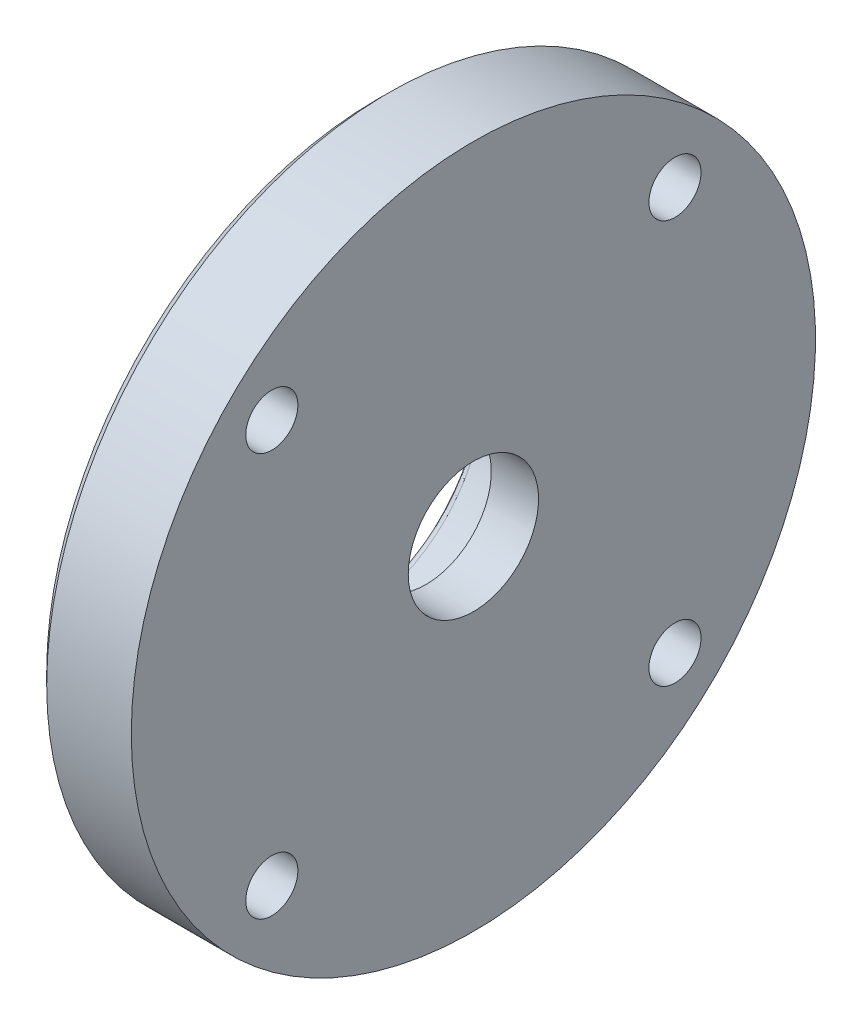
SolidWorks part; units mm, degrees
material "Chrome Stainless Steel"
ref_plane "Front" through (0, 0, 0) normal (0, 0, 1) x (1, 0, 0)
ref_plane "Top" through (0, 0, 0) normal (0, 1, 0) x (1, 0, 0)
ref_plane "Right" through (0, 0, 0) normal (1, 0, 0) x (0, 0, -1)
sketch "Sketch1" plane through (0, 0, 0) normal (0, 0, 1) x (1, 0, 0)
  line L0 (0, 0) -> (13.9806, 0) construction
  line L1 (0, 0) -> (0, 20.2929)
  line L2 (0, 20.2929) -> (0.7071, 21)
  line L3 (0.7071, 21) -> (5.9, 21)
  line L4 (5.9, 21) -> (5.9, 0)
  line L5 (0, 0) -> (5.9, 0)
  dimension "D1" = 5.9
  dimension "D2" = 21
  dimension "D3" = 135
  dimension "D4" = 1
revolve "Revolve1" add sketch "Sketch1" angle 360 about L0
sketch "Sketch2" plane through (0, 0, 0) normal (-1, 0, 0) x (0, 0, 1)
  line L2 (-11.5, -4.899) -> (-11.5, 4.899)
  line L4 (11.5, -4.899) -> (11.5, 4.899)
  arc A0 (11.5, 4.899) -> (-11.5, 4.899) centre (0, 0) ccw
  arc A1 (-11.5, -4.899) -> (11.5, -4.899) centre (0, 0) ccw
  circle A2 centre (0, 0) radius 8
  dimension "D2" = 12.5
  dimension "D3" = 16
  dimension "D1" = 23
extrude "Boss-Extrude1" add sketch "Sketch2" along normal blind 2
fillet "Fillet1" radius 0.5 13 edges at (0, 0, -11.5) (-1, -4.899, -11.5) (0, -12.5, 0) (-1, -4.899, 11.5) (0, 0, 11.5) (-1, 4.899, 11.5) (-1, 4.899, -11.5) (0, 12.5, 0) (-2, 0, 8) (-2, 0, 11.5) (-2, -12.5, 0) (-2, 0, -11.5) (-2, 12.5, 0)
sketch "Sketch3" plane through (0, 0, 0) normal (-1, 0, 0) x (0, 0, 1)
  line L0 (0, 0) -> (12.3744, 12.3744) construction
  line L1 (0, 0) -> (17.5, 0) construction
  circle A0 centre (0, 0) radius 17.5 construction
  circle A1 centre (12.3744, 12.3744) radius 1.6
  circle A2 centre (-12.3744, 12.3744) radius 1.6
  circle A3 centre (-12.3744, -12.3744) radius 1.6
  circle A4 centre (12.3744, -12.3744) radius 1.6
  point P15 (0, 0)
  dimension "D1" = 35
  dimension "D3" = 3.2
  dimension "D2" = 45
  dimension "D4" = 4
extrude "Cut-Extrude1" cut sketch "Sketch3" against normal blind 10
sketch "Sketch4" plane through (0, 0, 0) normal (-1, 0, 0) x (0, 0, 1)
  circle A0 centre (0, 0) radius 4
extrude "Cut-Extrude2" cut sketch "Sketch4" against normal blind 10 contours A0
sketch "Sketch5" plane through (0, 0, 0) normal (-1, 0, 0) x (0, 0, 1)
  circle A0 centre (0, 0) radius 8
extrude "Cut-Extrude3" cut sketch "Sketch5" along direction (-1, 0, 0) on the side against the normal offset from surface (3 mm away) 5
